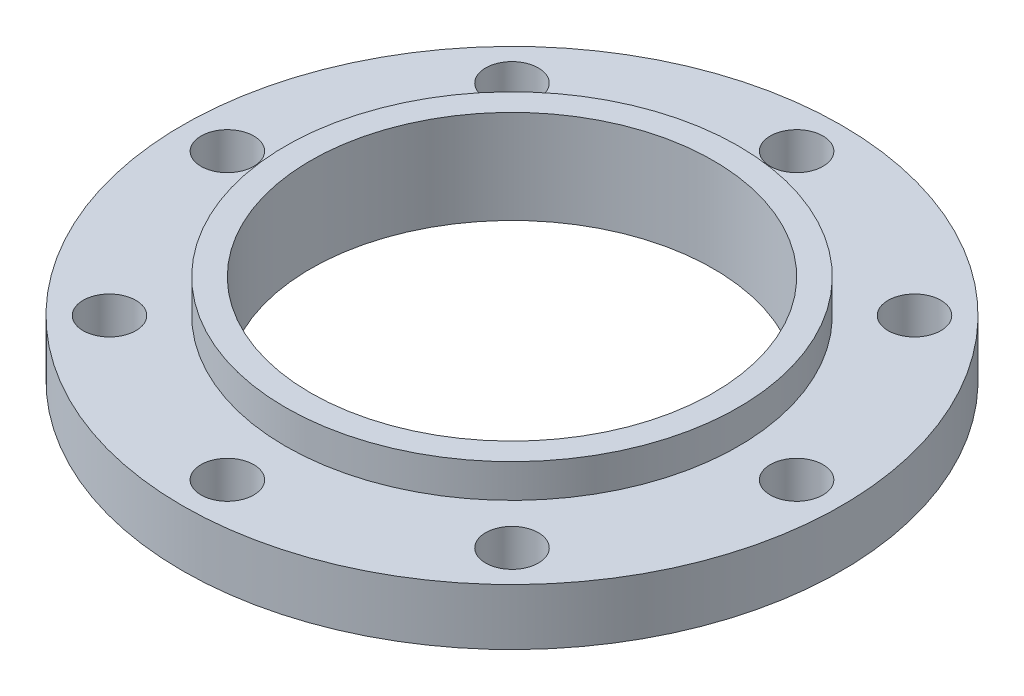
SolidWorks part; units mm, degrees
ref_plane "Front Plane" through (0, 0, 0) normal (0, 0, 1) x (1, 0, 0)
ref_plane "Top Plane" through (0, 0, 0) normal (0, 1, 0) x (1, 0, 0)
ref_plane "Right Plane" through (0, 0, 0) normal (1, 0, 0) x (0, 0, -1)
sketch "Sketch1" plane through (0, 0, 0) normal (0, 1, 0) x (1, 0, 0)
  circle A0 centre (0, 0) radius 5.5
  dimension "D1" = 11
extrude "Boss-Extrude1" add sketch "Sketch1" along normal blind 0.94
sketch "Sketch3" plane through (0, 0, 0) normal (0, 1, 0) x (1, 0, 0)
  circle A0 centre (0, 0) radius 3.78
  dimension "D1" = 7.56
extrude "Boss-Extrude2" add sketch "Sketch3" along normal blind 1.5
sketch "Sketch4" plane through (0, 0, 0) normal (0, 1, 0) x (1, 0, 0)
  circle A0 centre (0, 0) radius 4.25
  dimension "D1" = 8.5
extrude "Boss-Extrude3" add sketch "Sketch4" against normal blind 0.0625
sketch "Sketch5" plane through (0, 0, 0) normal (0, 1, 0) x (1, 0, 0)
  circle A0 centre (0, 0) radius 3.36
  dimension "D1" = 6.72
extrude "Cut-Extrude1" cut sketch "Sketch5" against normal blind 6.0625 and the other way blind 20 contours A0
sketch "Sketch6" plane through (0, 0, 0) normal (0, 0, 1) x (1, 0, 0)
  line L0 (0, -0.1942) -> (0, 2.034) construction
  line L1 (6.05, 0) -> (-6.05, 0) construction
sketch "Sketch7" plane through (0, 0, 0) normal (0, 1, 0) x (1, 0, 0)
  circle A0 centre (0, 4.75) radius 0.44
  dimension "D2" = 4.75
  dimension "D1" = 0.88
extrude "Cut-Extrude2" cut sketch "Sketch7" along normal blind 7.0625
pattern_circular "CirPattern1" count 8 over 360 about axis through (0, 0, 0) along (0, 1, 0) of "Cut-Extrude2"
scale "Scale1" scale about centroid uniform scaling yes scale factor 25.4
